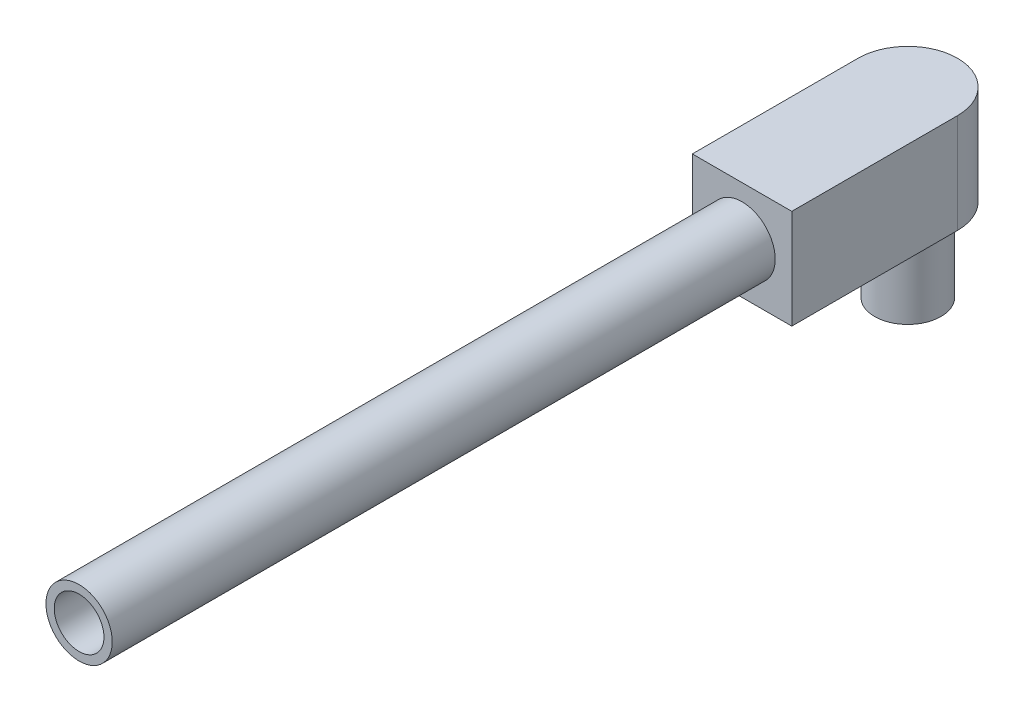
SolidWorks part; units mm, degrees
ref_plane "前视基准面" through (0, 0, 0) normal (0, 0, 1) x (1, 0, 0)
ref_plane "上视基准面" through (0, 0, 0) normal (0, 1, 0) x (1, 0, 0)
ref_plane "右视基准面" through (0, 0, 0) normal (1, 0, 0) x (0, 0, -1)
sketch "草图1" plane through (0, 0, 0) normal (0, 0, 1) x (1, 0, 0)
  line L1 (15, -15) -> (-15, -15)
  line L2 (15, -15) -> (15, 15)
  line L3 (15, 15) -> (-15, 15)
  line L4 (-15, -15) -> (-15, 15)
  line L5 (15, -15) -> (-15, 15) construction
  line L6 (15, 15) -> (-15, -15) construction
  point P0 (0, 0)
  dimension "D3" = 30
extrude "凸台-拉伸1" add sketch "草图1" along normal blind 5
sketch "草图2" plane through (0, 0, 5) normal (0, 0, 1) x (1, 0, 0)
  circle A0 centre (0, 0) radius 10
  circle A1 centre (0, 0) radius 7.5
  dimension "D1" = 15
  dimension "D2" = 20
extrude "凸台-拉伸2" add sketch "草图2" along normal blind 200 contours A1 | A0
sketch "草图3" plane through (0, 0, 0) normal (0, 0, -1) x (-1, 0, 0)
  line L0 (-15, 15) -> (15, 15)
  line L1 (15, 15) -> (15, -15)
  line L2 (15, 15) -> (15, -15) construction
  line L3 (15, -15) -> (-15, -15)
  line L4 (-15, -15) -> (-15, 15) construction
  line L5 (-15, -15) -> (-15, 15)
  dimension "D1" = 30
extrude "凸台-拉伸3" add sketch "草图3" along normal blind 60
sketch "草图4" plane through (0, -15, 0) normal (0, -1, 0) x (1, 0, 0)
  line L1 (15, -60) -> (15, 5) construction
  line L3 (15, -60) -> (-15, -60) construction
  circle A0 centre (0, -45) radius 10
  circle A1 centre (0, -45) radius 18 construction
  dimension "D1" = 20
  dimension "D2" = 36
  dimension "D3" = 15
  dimension "D4" = 15
extrude "凸台-拉伸4" add sketch "草图4" along normal blind 25
sketch "草图5" plane through (0, -15, 0) normal (0, -1, 0) x (1, 0, 0)
  line L0 (15, -45) -> (15, -76.8705)
  line L1 (15, -76.8705) -> (-15, -76.8705)
  line L2 (-15, -76.8705) -> (-15, -45)
  line L3 (-15, -60) -> (-15, 5) construction
  arc A0 (-15, -45) -> (15, -45) centre (0, -45) ccw
extrude "切除-拉伸1" cut sketch "草图5" against normal through all
